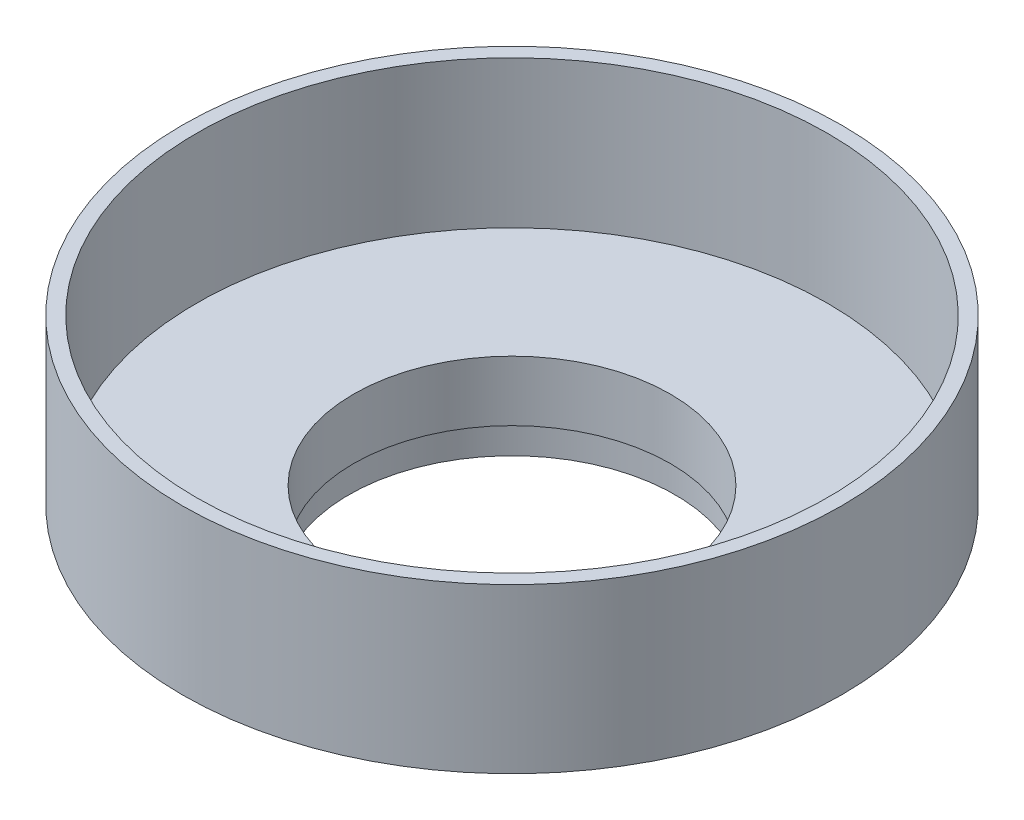
SolidWorks part; units mm, degrees
ref_plane "Front Plane" through (0, 0, 0) normal (0, 0, 1) x (1, 0, 0)
ref_plane "Top Plane" through (0, 0, 0) normal (0, 1, 0) x (1, 0, 0)
ref_plane "Right Plane" through (0, 0, 0) normal (1, 0, 0) x (0, 0, -1)
sketch "Sketch1" plane through (0, 0, 0) normal (0, 0, 1) x (1, 0, 0)
  line L0 (0, 0) -> (68.072, 0) construction
  line L1 (80.01, 12.9453) -> (80.01, -34.9083) construction
  line L2 (34.163, -31.7587) -> (34.163, -44.7381)
  line L3 (0, -31.7587) -> (34.163, -31.7587) construction
  line L4 (35.5564, -51.0881) -> (35.5564, -44.4841)
  line L6 (80.01, -34.9083) -> (35.5564, -51.0881) construction
  line L7 (34.163, -31.7587) -> (68.072, -31.7587)
  line L8 (71.12, -35.3256) -> (68.6542, -36.2231)
  line L9 (68.6542, -36.2231) -> (34.7624, -36.2231)
  line L10 (34.7624, -44.4841) -> (34.7624, -36.2231)
  line L11 (0, 0) -> (0, -64.008) construction
  line L12 (34.163, -44.7381) -> (35.1869, -44.7381)
  line L13 (34.7624, -44.4841) -> (35.5564, -44.4841)
  line L14 (35.1869, -44.7381) -> (35.1869, -51.0881)
  line L15 (71.12, 0) -> (71.12, -35.3256)
  line L16 (35.1869, -51.0881) -> (35.5564, -51.0881)
  line L21 (68.072, -31.7587) -> (68.072, 0)
  line L22 (71.12, 0) -> (68.072, 0)
  dimension "D1" = 71.12
  dimension "D2" = 70
  dimension "D3" = 64.0334
  dimension "D5" = 6.35
  dimension "D4" = 34.163
  dimension "D6" = 0.254
  dimension "D7" = 68.072
  dimension "D8" = 80.01
  dimension "D9" = 47.8536
  dimension "D10" = 44.704
revolve "Revolve1" add sketch "Sketch1" angle 360 about L11
